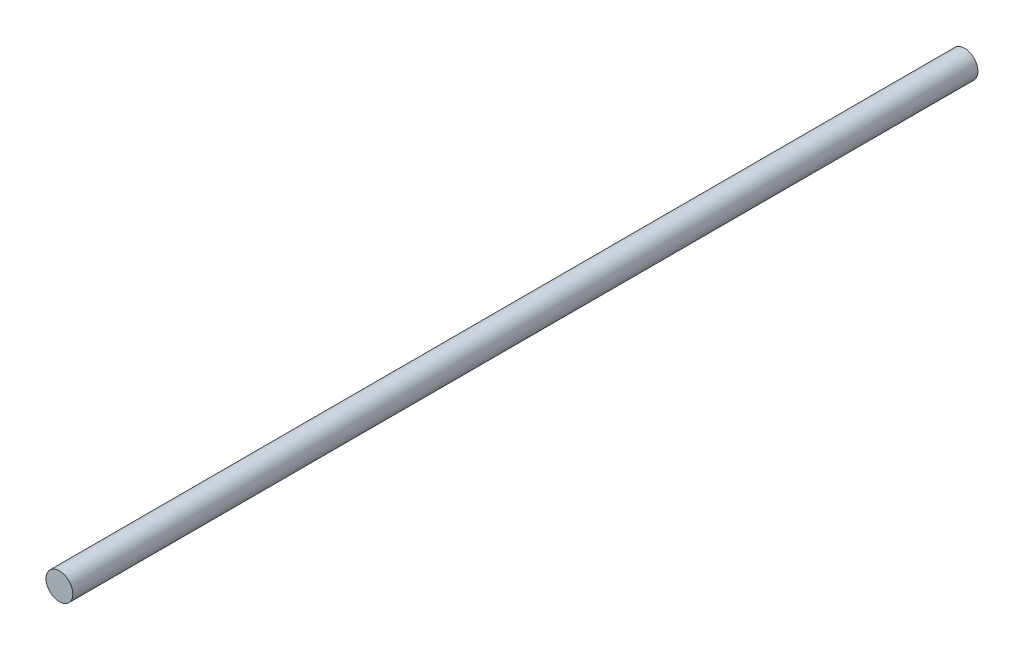
SolidWorks part; units mm, degrees
ref_plane "Front Plane" through (0, 0, 0) normal (0, 0, 1) x (1, 0, 0)
ref_plane "Top Plane" through (0, 0, 0) normal (0, 1, 0) x (1, 0, 0)
ref_plane "Right Plane" through (0, 0, 0) normal (1, 0, 0) x (0, 0, -1)
sketch "Sketch1" plane through (0, 0, 0) normal (0, 0, 1) x (1, 0, 0)
  circle A0 centre (0, 0) radius 4.7625
extrude "Boss-Extrude1" add sketch "Sketch1" along normal blind 321.31
